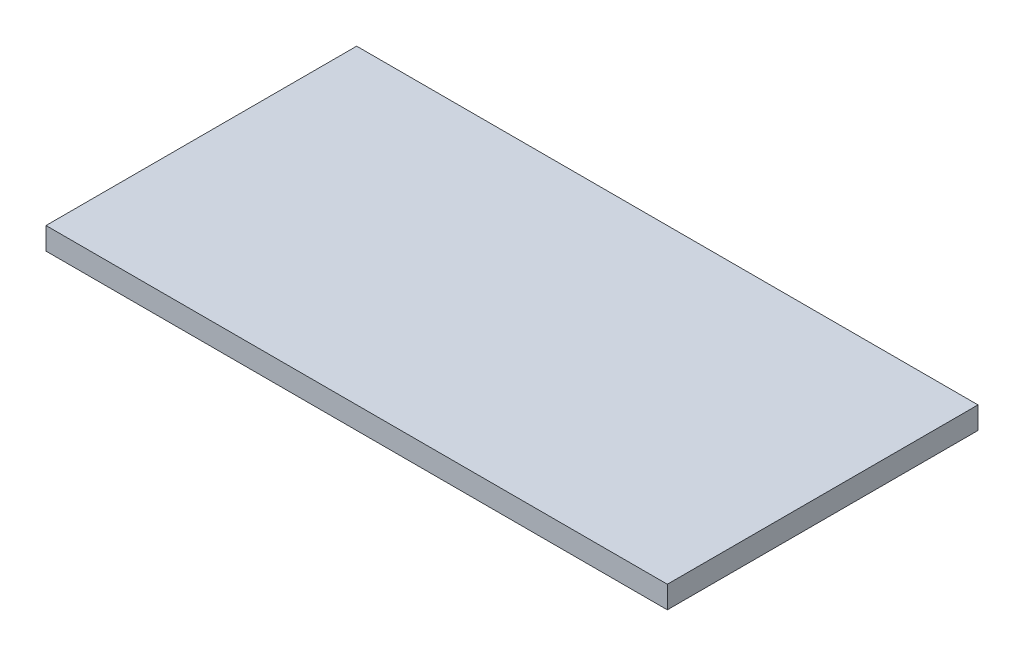
SolidWorks part; units mm, degrees
ref_plane "Front" through (0, 0, 0) normal (0, 0, 1) x (1, 0, 0)
ref_plane "Top" through (0, 0, 0) normal (0, 1, 0) x (1, 0, 0)
ref_plane "Right" through (0, 0, 0) normal (1, 0, 0) x (0, 0, -1)
sketch "Sketch1" plane through (0, 0, 0) normal (0, 1, 0) x (1, 0, 0)
  line L1 (0, 0) -> (88.9, 0)
  line L2 (0, 0) -> (0, -44.45)
  line L3 (0, -44.45) -> (88.9, -44.45)
  line L4 (88.9, 0) -> (88.9, -44.45)
  dimension "D1" = 44.45
  dimension "D2" = 88.9
extrude "Boss-Extrude1" add sketch "Sketch1" along normal blind 3.175
